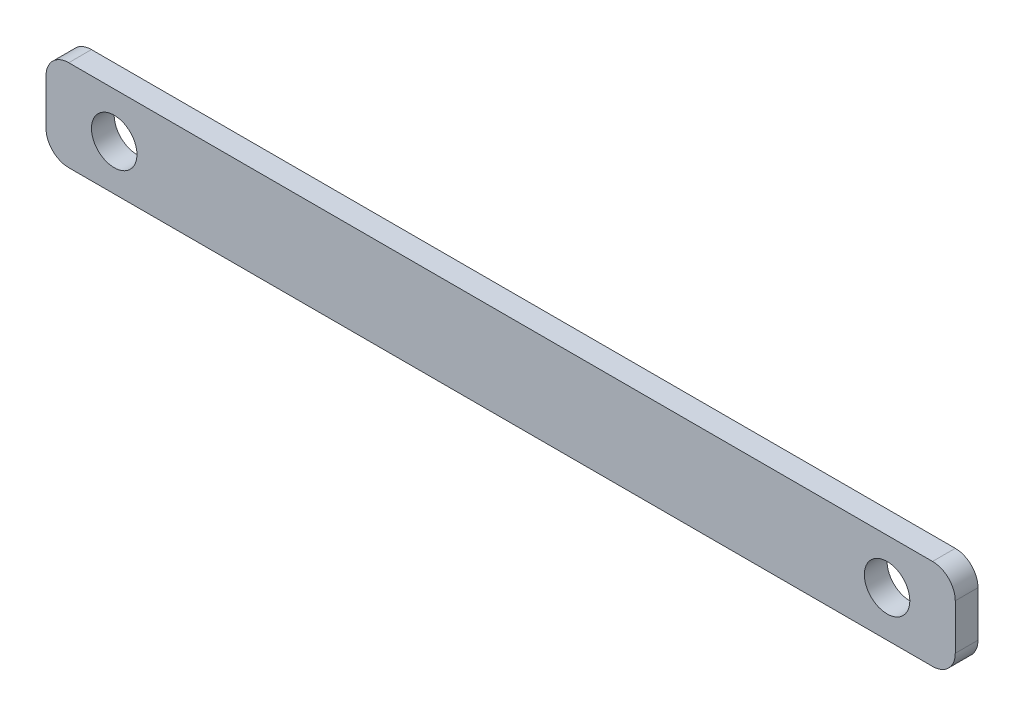
SolidWorks part; units mm, degrees
ref_plane "Front Plane" through (0, 0, 0) normal (0, 0, 1) x (1, 0, 0)
ref_plane "Top Plane" through (0, 0, 0) normal (0, 1, 0) x (1, 0, 0)
ref_plane "Right Plane" through (0, 0, 0) normal (1, 0, 0) x (0, 0, -1)
sketch "Sketch1" plane through (0, 0, 0) normal (0, 0, 1) x (1, 0, 0)
  line L0 (-200, 151.0182) -> (-170, 151.0182) construction
  line L1 (-275.7696, 0) -> (293.3567, 0) construction
  line L2 (-190, 151.0182) -> (190, 151.0182)
  line L3 (-200, 141.0182) -> (-200, 121.0182)
  line L4 (-190, 111.0182) -> (190, 111.0182)
  line L5 (200, 141.0182) -> (200, 121.0182)
  line L6 (-200, 151.0182) -> (200, 111.0182) construction
  line L7 (-200, 111.0182) -> (200, 151.0182) construction
  line L8 (200, 151.0182) -> (170, 151.0182) construction
  line L9 (-170, 151.0182) -> (-170, 111.0182) construction
  line L10 (170, 151.0182) -> (170, 111.0182) construction
  arc A0 (190, 111.0182) -> (200, 121.0182) centre (190, 121.0182) ccw
  arc A1 (190, 151.0182) -> (200, 141.0182) centre (190, 141.0182) cw
  arc A2 (-200, 121.0182) -> (-190, 111.0182) centre (-190, 121.0182) ccw
  arc A3 (-190, 151.0182) -> (-200, 141.0182) centre (-190, 141.0182) ccw
  circle A4 centre (-170, 131.0182) radius 10
  circle A5 centre (170, 131.0182) radius 10
  point P0 (0, 131.0182)
  dimension "D3" = 10
  dimension "D1" = 400
  dimension "D2" = 40
extrude "Boss-Extrude1" add sketch "Sketch1" along normal mid plane 10
